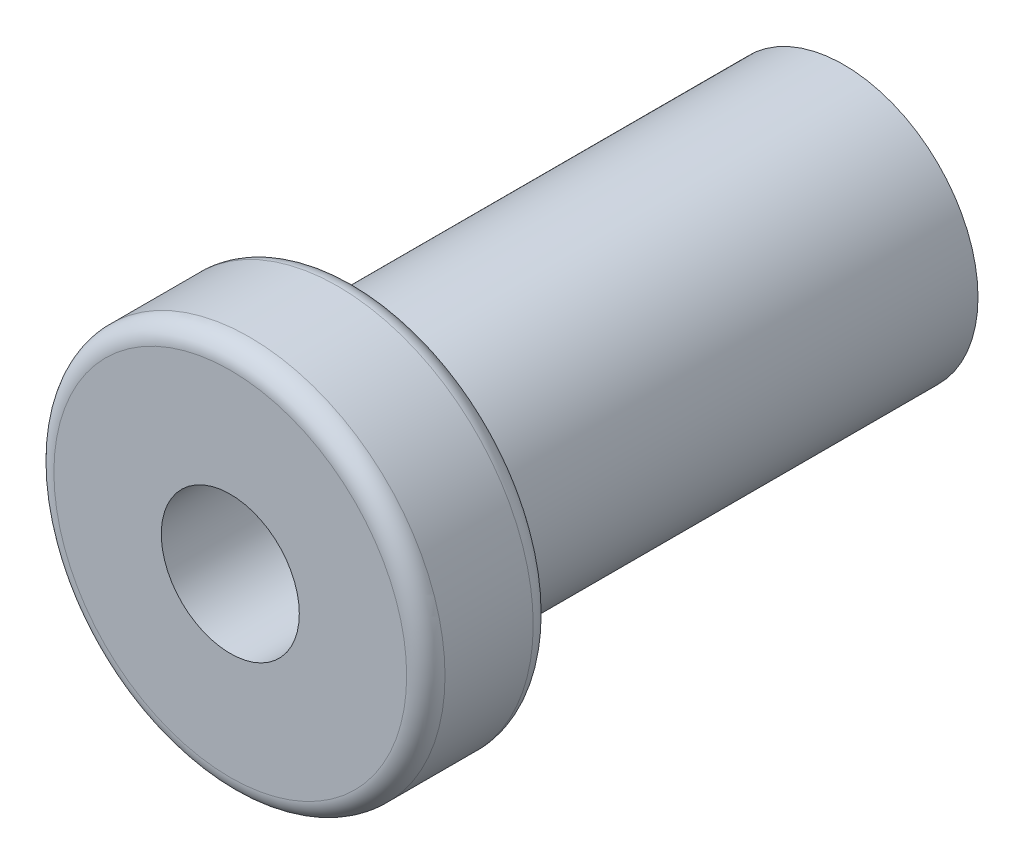
SolidWorks part; units mm, degrees
ref_plane "Front Plane" through (0, 0, 0) normal (0, 0, 1) x (1, 0, 0)
ref_plane "Top Plane" through (0, 0, 0) normal (0, 1, 0) x (1, 0, 0)
ref_plane "Right Plane" through (0, 0, 0) normal (1, 0, 0) x (0, 0, -1)
sketch "Sketch1" plane through (0, 0, 0) normal (1, 0, 0) x (0, 0, -1)
  line L0 (0, 3.5) -> (0, -3.5) construction
  line L1 (-3.3, 5.1) -> (0, 5.1)
  line L2 (-3.3, 5.1) -> (-3.3, -5.1)
  line L3 (-3.3, -5.1) -> (0, -5.1)
  line L4 (0, 5.1) -> (0, 3.5)
  line L5 (-3.3, 5.1) -> (0, -5.1) construction
  line L6 (-3.3, -5.1) -> (0, 5.1) construction
  line L7 (12.7, 3.5) -> (0, 3.5)
  line L8 (12.7, 3.5) -> (12.7, -3.5)
  line L9 (12.7, -3.5) -> (0, -3.5)
  line L10 (0, 3.5) -> (0, -3.5) construction
  line L11 (12.7, 3.5) -> (0, -3.5) construction
  line L12 (12.7, -3.5) -> (0, 3.5) construction
  line L13 (0, -3.5) -> (0, -5.1)
  line L14 (0, 0) -> (50000, 0) construction
  line L15 (-3.3, 0) -> (12.7, 0)
  point P0 (-1.65, 0)
  point P5 (6.35, 0)
  point P17 (0, 0)
  dimension "D1" = 10.2
  dimension "D2" = 3.3
  dimension "D3" = 7
  dimension "D4" = 12.7
revolve "Revolve3" add sketch "Sketch1" angle 360 about L14
fillet "Fillet1" radius 0.5 2 edges at (5.1, 0, 0) (5.1, 0, 3.3)
sketch "Sketch2" plane through (0, 0, 3.3) normal (0, 0, 1) x (1, 0, 0)
  circle A0 centre (0, 0) radius 1.8
  dimension "D1" = 3.6
extrude "Cut-Extrude1" cut sketch "Sketch2" against normal blind 14
